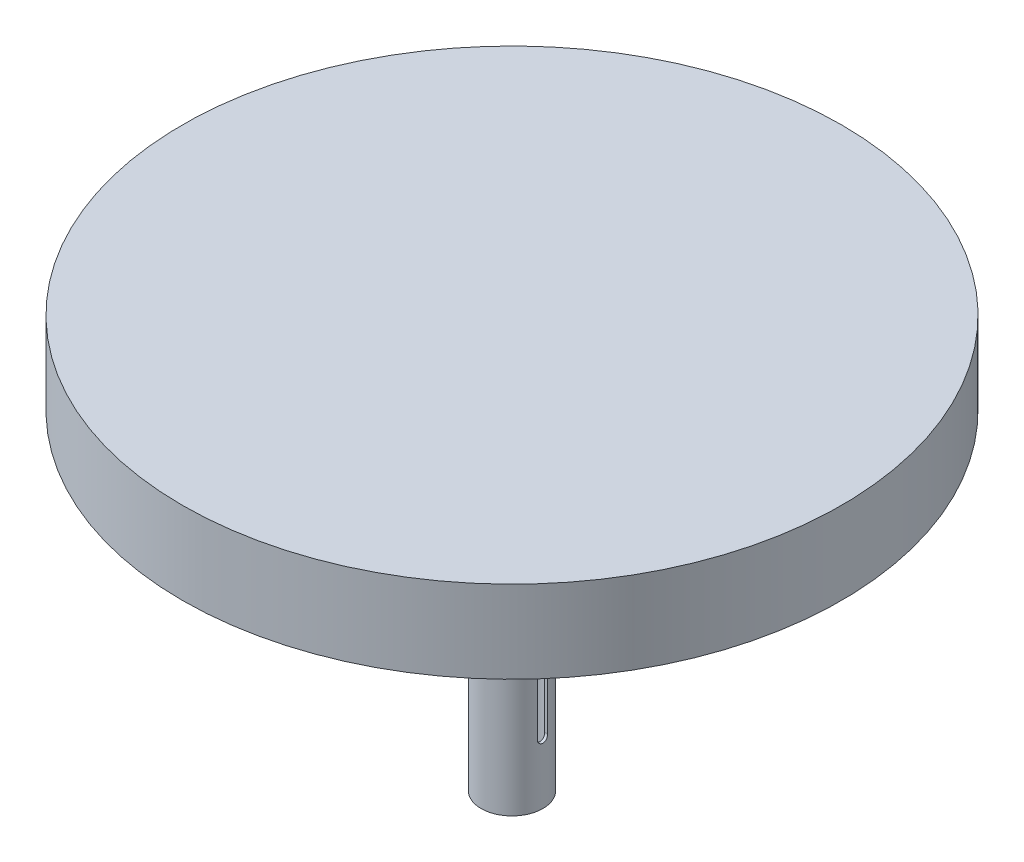
SolidWorks part; units mm, degrees
ref_plane "Front Plane" through (0, 0, 0) normal (0, 0, 1) x (1, 0, 0)
ref_plane "Top Plane" through (0, 0, 0) normal (0, 1, 0) x (1, 0, 0)
ref_plane "Right Plane" through (0, 0, 0) normal (1, 0, 0) x (0, 0, -1)
sketch "Sketch1" plane through (0, 0, 0) normal (0, 1, 0) x (1, 0, 0)
  circle A0 centre (0, 0) radius 101.6
  dimension "D1" = 203.2
extrude "Boss-Extrude1" add sketch "Sketch1" along normal blind 25.4
sketch "Sketch2" plane through (0, 0, 0) normal (0, -1, 0) x (1, 0, 0)
  circle A0 centre (0, 0) radius 9.525
  circle A1 centre (0, 0) radius 8.636
  dimension "D1" = 19.05
  dimension "D2" = 0.889
extrude "Boss-Extrude2" add sketch "Sketch2" along normal blind 101.6
sketch "Sketch3" plane through (0, 0, 0) normal (0, 0, 1) x (1, 0, 0)
  line L0 (-9.525, -101.6) -> (9.525, -101.6) construction
  circle A0 centre (0, -12.7) radius 2.3812
  dimension "D2" = 4.7625
  dimension "D1" = 88.9
  dimension "D3" = 9.525
extrude "Cut-Extrude1" cut sketch "Sketch3" against normal through all and the other way through all
sketch "Sketch4" plane through (0, 0, 0) normal (1, 0, 0) x (0, 0, -1)
  line L0 (0, -82.55) -> (0, -57.15) construction
  line L1 (-1.5875, -82.55) -> (-1.5875, -57.15)
  line L2 (1.5875, -82.55) -> (1.5875, -57.15)
  line L3 (-9.525, -101.6) -> (9.525, -101.6) construction
  arc A0 (-1.5875, -82.55) -> (1.5875, -82.55) centre (0, -82.55) ccw
  arc A1 (1.5875, -57.15) -> (-1.5875, -57.15) centre (0, -57.15) ccw
  point P3 (0, -69.85)
  dimension "D1" = 25.4
  dimension "D2" = 3.175
  dimension "D3" = 19.05
extrude "Cut-Extrude2" cut sketch "Sketch4" against normal blind 25.4 and the other way blind 25.908
